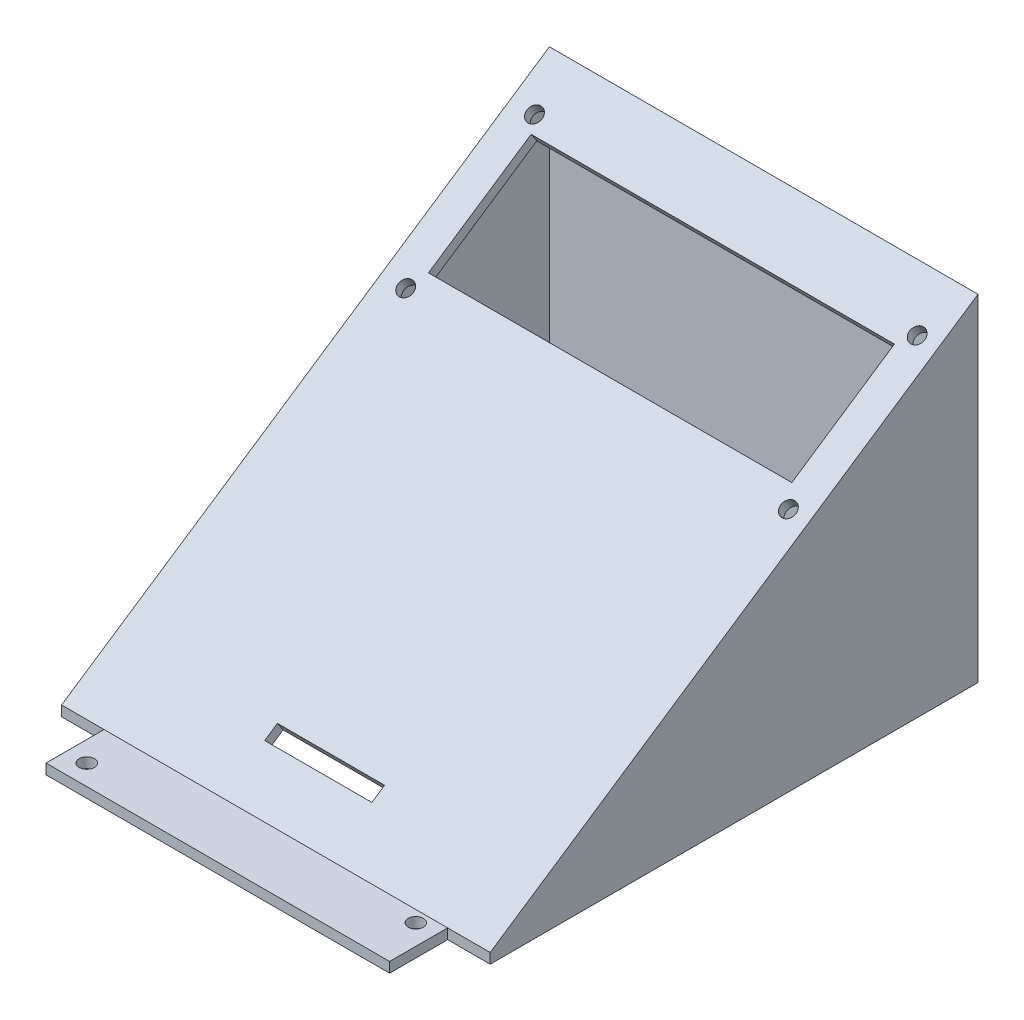
SolidWorks part; units mm, degrees
ref_plane "Front" through (0, 0, 0) normal (0, 0, 1) x (1, 0, 0)
ref_plane "Top" through (0, 0, 0) normal (0, 1, 0) x (1, 0, 0)
ref_plane "Right" through (0, 0, 0) normal (1, 0, 0) x (0, 0, -1)
sketch "Sketch1" plane through (0, 0, 0) normal (0, 1, 0) x (1, 0, 0)
  line L0 (-64.6646, -72.5007) -> (-64.6646, -68.5007) construction
  line L1 (-92.3346, -123.0307) -> (-96.3346, -123.0307) construction
  line L2 (-36.9946, -121.4678) -> (-32.9946, -121.4678) construction
  line L3 (-92.1357, -177.5607) -> (-92.1357, -173.5607) construction
  line L4 (-98.3346, -179.5607) -> (-30.9946, -179.5607)
  line L9 (-92.3346, -72.5007) -> (-36.9946, -72.5007)
  line L10 (-92.3346, -72.5007) -> (-92.3346, -173.5607)
  line L11 (-92.3346, -173.5607) -> (-36.9946, -173.5607)
  line L12 (-36.9946, -72.5007) -> (-36.9946, -173.5607)
  line L13 (-30.9946, -66.5007) -> (-30.9946, -179.5607)
  line L14 (-98.3346, -66.5007) -> (-30.9946, -66.5007)
  line L15 (-98.3346, -66.5007) -> (-98.3346, -179.5607)
  circle A0 centre (-34.9946, -70.5007) radius 1.5
  circle A1 centre (-94.3346, -70.5007) radius 1.5
  circle A2 centre (-94.3346, -175.5607) radius 1.5
  circle A3 centre (-34.9946, -170.4349) radius 1.5
  point P8 (-92.1357, -175.5607)
  point P9 (-64.6646, -70.5007)
  point P14 (-94.3346, -123.0307)
  point P17 (-34.9946, -121.4678)
  dimension "D2" = 3
  dimension "D1" = 113.06
extrude "Boss-Extrude1" add sketch "Sketch1" along normal blind 2
ref_plane "Plane1" through (-64.6646, 0, 0) normal (1, 0, 0) x (0, 0, -1)
sketch "Sketch3" plane through (-64.6646, 0, 0) normal (1, 0, 0) x (0, 0, -1)
  line L0 (-168.1808, 2) -> (-161.5906, 2)
  line L2 (-72.5773, 2) -> (-72.5773, 65.9137)
  line L3 (-72.5773, 65.9137) -> (-168.1808, 2)
  line L4 (-74.5773, 62.1709) -> (-161.5906, 4)
  line L6 (-74.5773, 4) -> (-74.5773, 62.1709)
  line L7 (-161.5906, 4) -> (-74.5773, 4) construction
  line L8 (-74.5773, 4) -> (-74.5773, 2)
  line L9 (-74.5773, 2) -> (-72.5773, 2)
  line L10 (-161.5906, 4) -> (-161.5906, 2)
  line L11 (-161.5906, 2) -> (-168.1808, 2)
  line L12 (-74.5773, 2) -> (-72.5773, 2)
  line L13 (-168.1808, 2) -> (-72.5773, 2) construction
  point P2 (-72.5007, 2)
  point P3 (-72.5773, 2)
  point P6 (-72.9857, 2)
  point P12 (-72.5183, 2)
  point P15 (0, 0)
  dimension "D1" = 115
  dimension "D2" = 2
extrude "Boss-Extrude2" add sketch "Sketch3" along normal mid plane 84 contours L10 L4 L6 L8 L9 L2 L3 L0
sketch "Sketch4" plane through (0, 0, 173.5607) normal (0, 0, -1) x (-1, 0, 0)
  line L5 (36.9946, 2) -> (92.3346, 2)
  line L6 (36.9946, 2) -> (36.9946, 0)
  line L7 (36.9946, 0) -> (92.3346, 0)
  line L8 (92.3346, 2) -> (92.3346, 0)
extrude "Boss-Extrude5" add sketch "Sketch4" along normal up to surface (11.9701 mm away) up to face at (-64.6646, 2.5, 161.5906)
sketch "Sketch5" plane through (0, 79.0872, 52.872) normal (0, 0.8313, 0.5558) x (1, 0, 0)
  line L0 (-64.6646, -50) -> (-64.6646, 50) construction
  line L1 (-100.2646, -35.7031) -> (-29.0646, -35.7031)
  line L2 (-100.2646, -35.7031) -> (-100.2646, -59.9031)
  line L3 (-100.2646, -59.9031) -> (-29.0646, -59.9031)
  line L4 (-29.0646, -35.7031) -> (-29.0646, -59.9031)
  line L5 (-22.6646, -23.7031) -> (-106.6646, -23.7031) construction
  line L6 (-30.9946, -138.7031) -> (-98.3346, -138.7031) construction
  line L7 (-75.1646, -125.7031) -> (-54.1646, -125.7031)
  line L8 (-75.1646, -125.7031) -> (-75.1646, -128.7031)
  line L9 (-75.1646, -128.7031) -> (-54.1646, -128.7031)
  line L10 (-54.1646, -125.7031) -> (-54.1646, -128.7031)
  circle A0 centre (-26.8246, -33.0331) radius 1.5
  circle A1 centre (-26.8246, -63.4031) radius 1.5
  circle A2 centre (-101.8246, -63.4031) radius 1.5
  circle A3 centre (-101.8246, -33.0331) radius 1.5
  point P4 (-64.6646, -35.7031)
  point P17 (-64.6646, -125.7031)
  dimension "D5" = 3
  dimension "D1" = 71.2
  dimension "D2" = 24.2
  dimension "D3" = 12
  dimension "D4" = 1.56
  dimension "D6" = 2.67
  dimension "D7" = 3.5
  dimension "D8" = 75
  dimension "D9" = 21
  dimension "D10" = 3
  dimension "D11" = 10
extrude "Cut-Extrude1" cut sketch "Sketch5" against normal up to next
sketch "Sketch6" plane through (-22.6646, 0, 0) normal (1, 0, 0) x (0, 0, -1)
  line L0 (-168.1808, 2) -> (-168.1808, 0)
  line L2 (-168.1808, 0) -> (-72.5773, 0)
  line L3 (-72.5773, 2) -> (-72.5773, 0)
  line L7 (-161.5906, 2) -> (-161.5906, 4)
  line L8 (-161.5906, 4) -> (-74.5773, 62.1709)
  line L9 (-74.5773, 62.1709) -> (-74.5773, 2)
  line L10 (-74.5773, 2) -> (-72.5773, 2)
  line L11 (-72.5773, 2) -> (-72.5773, 65.9137)
  line L12 (-72.5773, 65.9137) -> (-168.1808, 2)
  line L13 (-168.1808, 2) -> (-161.5906, 2)
  line L18 (-72.5773, 2) -> (-72.5773, 65.9137)
  line L19 (-72.5773, 65.9137) -> (-168.1808, 2)
  dimension "D1" = 0
extrude "Boss-Extrude6" add sketch "Sketch6" against normal blind 2
sketch "Sketch7" plane through (0, 2, 0) normal (0, -1, 0) x (1, 0, 0)
  line L1 (-24.6646, 168.1808) -> (-32.9946, 168.1808)
  line L2 (-24.6646, 168.1808) -> (-24.6646, 72.5773)
  line L3 (-24.6646, 72.5773) -> (-32.9946, 72.5773)
  line L4 (-32.9946, 168.1808) -> (-32.9946, 72.5773)
  point P6 (0, 0)
  point P7 (-24.6646, 72.5773)
extrude "Boss-Extrude7" add sketch "Sketch7" along normal up to surface (2 mm away) up to face at (-34.9946, 0, 171.9349)
mirror "Mirror1" about plane through (-64.6646, 0, 0) normal (1, 0, 0) of "Boss-Extrude6", "Boss-Extrude7"
sketch "Sketch8" plane through (0, 0, 72.5007) normal (0, 0, 1) x (1, 0, 0)
  line L4 (-92.3346, 0) -> (-36.9946, 0)
  line L5 (-36.9946, 0) -> (-36.9946, 2)
  line L6 (-92.3346, 0) -> (-36.9946, 0)
  line L7 (-92.3346, 2) -> (-92.3346, 0)
  line L9 (-36.9946, 0) -> (-36.9946, 2)
  line L11 (-92.3346, 2) -> (-92.3346, 0)
  line L12 (-36.9946, 2) -> (-92.3346, 2)
  line L13 (-36.9946, 2) -> (-92.3346, 2)
  dimension "D1" = 0
extrude "Boss-Extrude8" add sketch "Sketch8" along normal up to surface (2.0766 mm away) up to face at (-64.6646, 22.057, 74.5773)
